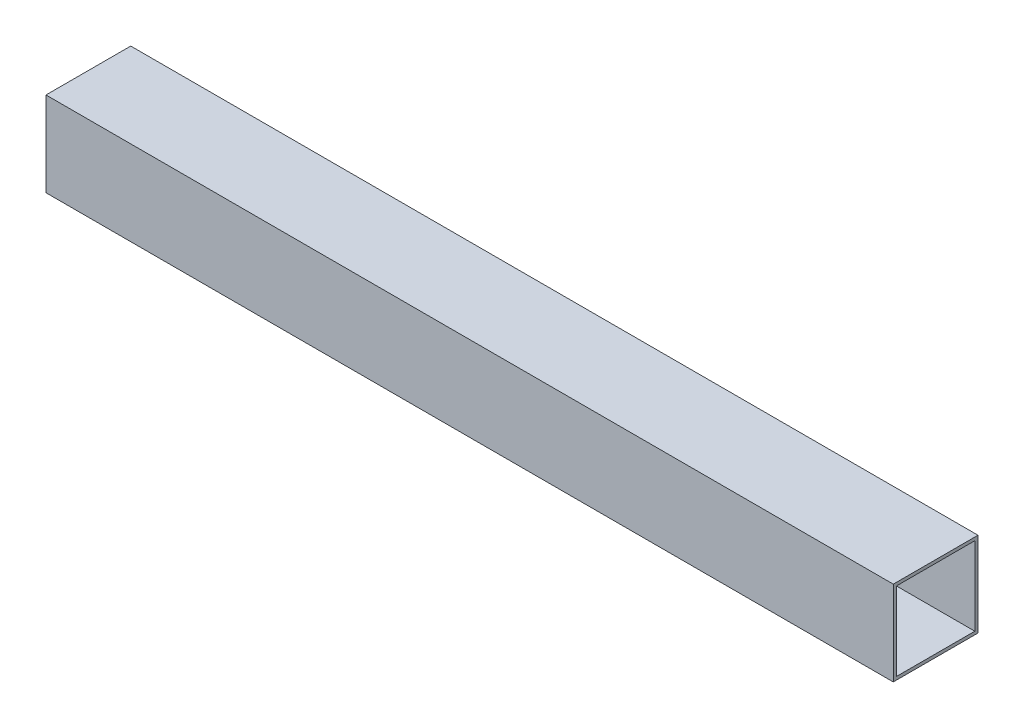
SolidWorks part; units mm, degrees
material "AISI 1020"
ref_plane "Plano frontal" through (0, 0, 0) normal (0, 0, 1) x (1, 0, 0)
ref_plane "Plano superior" through (0, 0, 0) normal (0, 1, 0) x (1, 0, 0)
ref_plane "Plano direito" through (0, 0, 0) normal (1, 0, 0) x (0, 0, -1)
sketch "Esboço1" plane through (0, 0, 0) normal (1, 0, 0) x (0, 0, -1)
  line L1 (-20, -20) -> (20, -20)
  line L2 (-20, -20) -> (-20, 20)
  line L3 (-20, 20) -> (20, 20)
  line L4 (20, -20) -> (20, 20)
  line L5 (-20, -20) -> (20, 20) construction
  line L6 (-20, 20) -> (20, -20) construction
  point P0 (0, 0)
  dimension "D1" = 40
  dimension "D2" = 40
extrude "Ressalto-extrusão1" add sketch "Esboço1" along normal blind 400
sketch "Esboço2" plane through (0, 0, 0) normal (-1, 0, 0) x (0, 0, 1)
  line L1 (-18.5, -18.5) -> (18.5, -18.5)
  line L2 (-18.5, -18.5) -> (-18.5, 18.5)
  line L3 (-18.5, 18.5) -> (18.5, 18.5)
  line L4 (18.5, -18.5) -> (18.5, 18.5)
  line L5 (-18.5, -18.5) -> (18.5, 18.5) construction
  line L6 (-18.5, 18.5) -> (18.5, -18.5) construction
  point P0 (0, 0)
  dimension "D1" = 37
  dimension "D2" = 37
extrude "Corte-extrusão1" cut sketch "Esboço2" against normal through all
